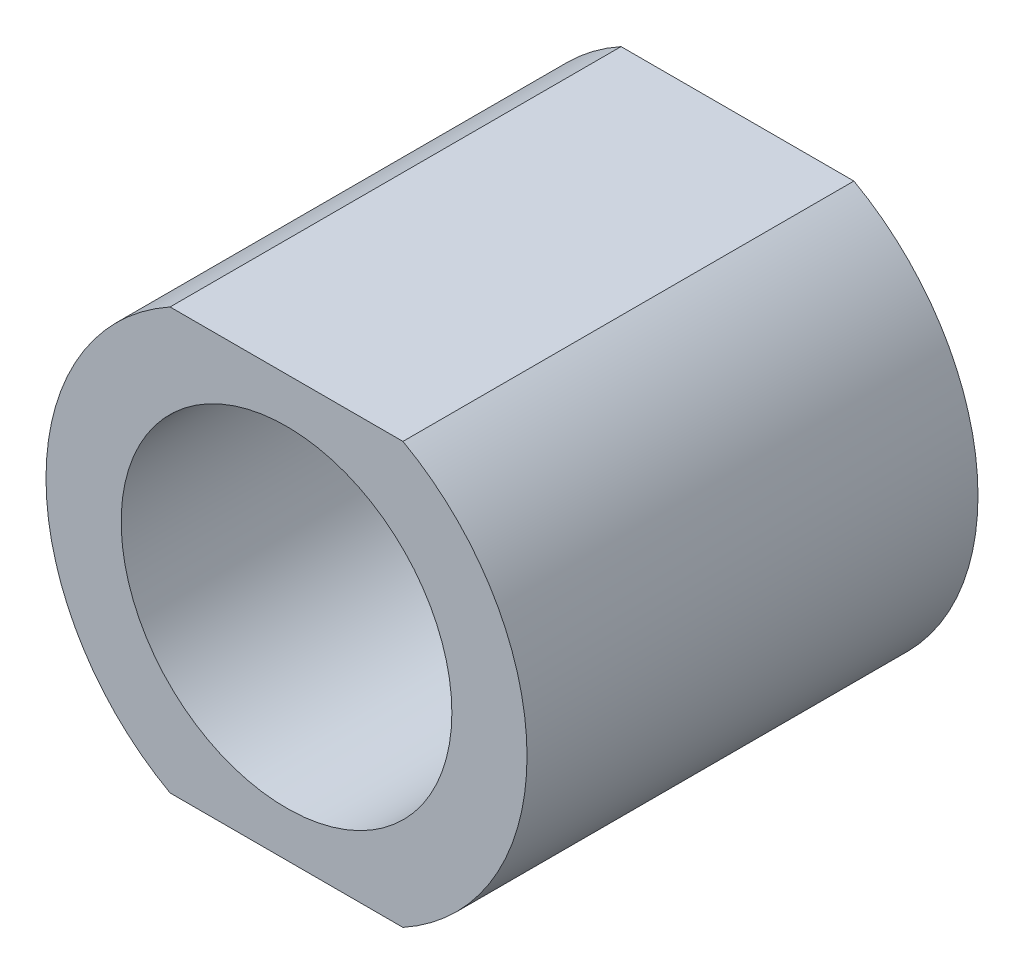
SolidWorks part; units mm, degrees
ref_plane "Piano frontale" through (0, 0, 0) normal (0, 0, 1) x (1, 0, 0)
ref_plane "Piano superiore" through (0, 0, 0) normal (0, 1, 0) x (1, 0, 0)
ref_plane "Piano destro" through (0, 0, 0) normal (1, 0, 0) x (0, 0, -1)
sketch "Schizzo2" plane through (0, 0, 0) normal (0, 0, 1) x (1, 0, 0)
  circle A0 centre (0, 0) radius 16
  circle A1 centre (0, 0) radius 11
  dimension "D1" = 22
  dimension "D2" = 32
extrude "Estrusione-Estrusione1" add sketch "Schizzo2" along normal blind 30
cosmetic thread "Filettatura cosmetica1" parameters "D2"=24
sketch "Schizzo3" plane through (0, 0, 30) normal (0, 0, 1) x (1, 0, 0)
  line L0 (0, 0) -> (-22.6268, 0) construction
  line L1 (-17.7945, 14) -> (22.432, 14)
  line L2 (-17.7945, 14) -> (-17.7945, 20.2426)
  line L3 (-17.7945, 20.2426) -> (22.432, 20.2426)
  line L4 (22.432, 14) -> (22.432, 20.2426)
  line L5 (-18.8635, -14) -> (24.0317, -14)
  line L6 (-18.8635, -14) -> (-18.8635, -22.1472)
  line L7 (-18.8635, -22.1472) -> (24.0317, -22.1472)
  line L8 (24.0317, -14) -> (24.0317, -22.1472)
  dimension "D1" = 28
extrude "Taglio-Estrusione1" cut sketch "Schizzo3" against normal through all
